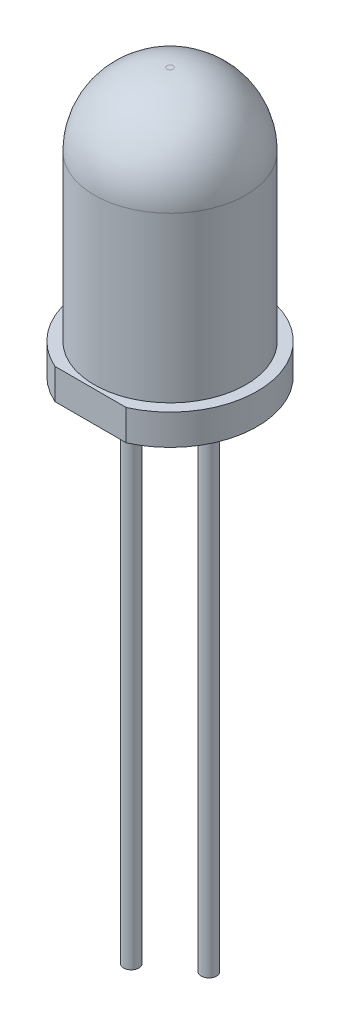
SolidWorks part; units mm, degrees
material "Perspex (TM) GS Acrylic Cast Sheet"
ref_plane "Front Plane" through (0, 0, 0) normal (0, 0, 1) x (1, 0, 0)
ref_plane "Top Plane" through (0, 0, 0) normal (0, 1, 0) x (1, 0, 0)
ref_plane "Right Plane" through (0, 0, 0) normal (1, 0, 0) x (0, 0, -1)
sketch "Sketch1" plane through (0, 0, 0) normal (0, 0, 1) x (1, 0, 0)
  line L0 (0, 0) -> (0, 8.75)
  line L1 (0, 0) -> (2.85, 0)
  line L2 (2.85, 0) -> (2.85, 1)
  line L3 (2.85, 1) -> (2.48, 1)
  line L4 (2.48, 1) -> (2.48, 6.37)
  line L5 (0, 8.75) -> (0.1, 8.75)
  arc A0 (2.48, 6.37) -> (0.1, 8.75) centre (0.1, 6.37) ccw
  dimension "D5" = 0.1
  dimension "D1" = 8.75
  dimension "D2" = 2.85
  dimension "D3" = 2.48
  dimension "D4" = 1
revolve "Revolve1" add sketch "Sketch1" angle 360 about L0
sketch "Sketch2" plane through (0, 0, 0) normal (0, -1, 0) x (1, 0, 0)
  line L0 (0, 0) -> (0, 2.6) construction
  line L1 (-1.1673, 2.6) -> (1.1673, 2.6)
  line L2 (0, 2.6) -> (0, 2.85) construction
  line L3 (0, 0) -> (0, -2.85) construction
  circle A0 centre (0, 0) radius 2.85 construction
  arc A1 (1.1673, 2.6) -> (-1.1673, 2.6) centre (0, 0) ccw
  dimension "D1" = 5.45
extrude "Cut-Extrude1" cut sketch "Sketch2" against normal up to surface (1 mm away) up to face at (0, 1, -2.48)
sketch "Sketch3" plane through (0, 0, 0) normal (0, -1, 0) x (1, 0, 0)
  line L0 (0, 1.27) -> (0, -1.27) construction
  circle A0 centre (0, -1.27) radius 0.25
  circle A1 centre (0, 1.27) radius 0.25
  dimension "D2" = 0.5
  dimension "D1" = 2.54
extrude "Boss-Extrude1" add sketch "Sketch3" along normal blind 16
sketch "Sketch4" plane through (0, -16, 0) normal (0, -1, 0) x (1, 0, 0)
  circle A0 centre (0, -1.27) radius 0.25 construction
  circle A1 centre (0, -1.27) radius 0.25
  circle A2 centre (0, 1.27) radius 0.25 construction
  circle A3 centre (0, 1.27) radius 0.25 construction
extrude "Boss-Extrude2" add sketch "Sketch4" along normal blind 1.5
